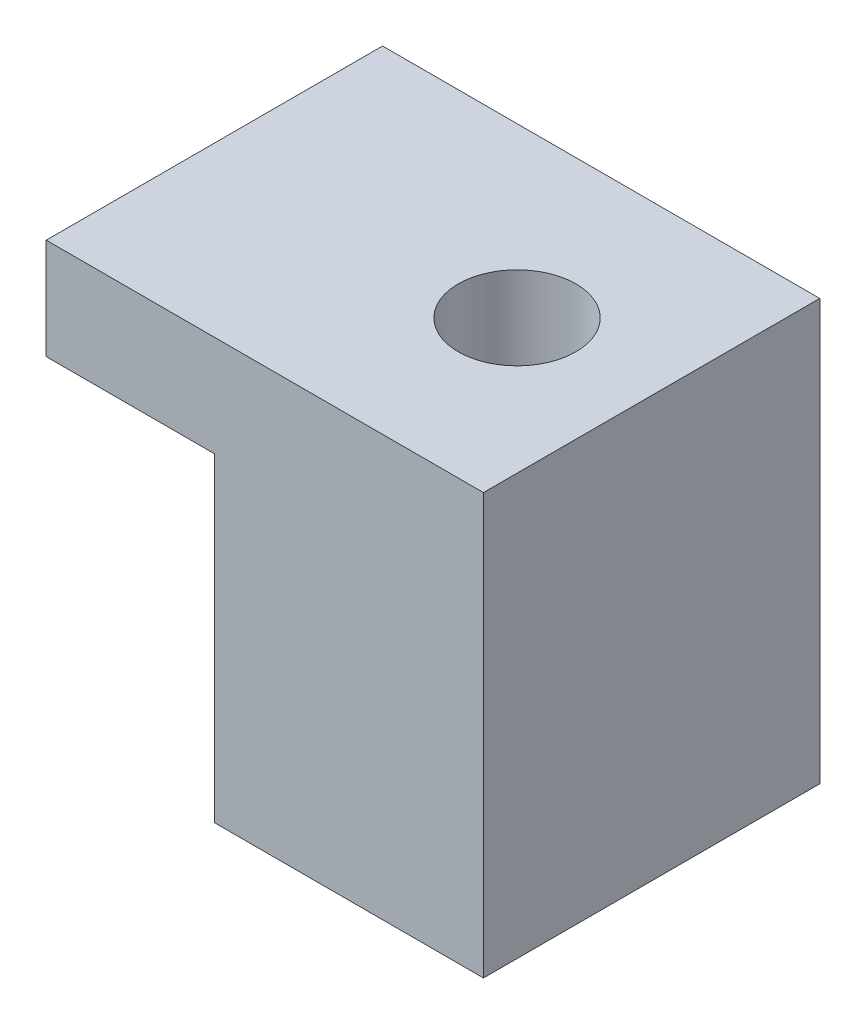
SolidWorks part; units mm, degrees
ref_plane "正面(Front)" through (0, 0, 0) normal (0, 0, 1) x (1, 0, 0)
ref_plane "平面(Top)" through (0, 0, 0) normal (0, 1, 0) x (1, 0, 0)
ref_plane "右側面(Right)" through (0, 0, 0) normal (1, 0, 0) x (0, 0, -1)
sketch "ｽｹｯﾁ1" plane through (0, 0, 0) normal (0, 0, 1) x (1, 0, 0)
  line L0 (0, 0) -> (0, 9.5)
  line L1 (0, 9.5) -> (-5, 9.5)
  line L2 (-5, 9.5) -> (-5, 12.5)
  line L3 (-5, 12.5) -> (8, 12.5)
  line L4 (8, 12.5) -> (8, 0)
  line L5 (8, 0) -> (0, 0)
  dimension "D1" = 8
  dimension "D2" = 9.5
  dimension "D3" = 3
  dimension "D4" = 5
extrude "ﾎﾞｽ - 押し出し1" add sketch "ｽｹｯﾁ1" along normal blind 10
sketch "ｽｹｯﾁ2" plane through (0, 0, 0) normal (0, -1, 0) x (1, 0, 0)
  line L0 (0, 0) -> (8, 0) construction
  line L1 (8, 10) -> (8, 0) construction
  circle A0 centre (4, 5) radius 1.75
  point P4 (4, 0)
  point P5 (0, 0)
  point P8 (8, 5)
  dimension "D1" = 3.5
extrude "ｶｯﾄ - 押し出し1" cut sketch "ｽｹｯﾁ2" against normal through all
